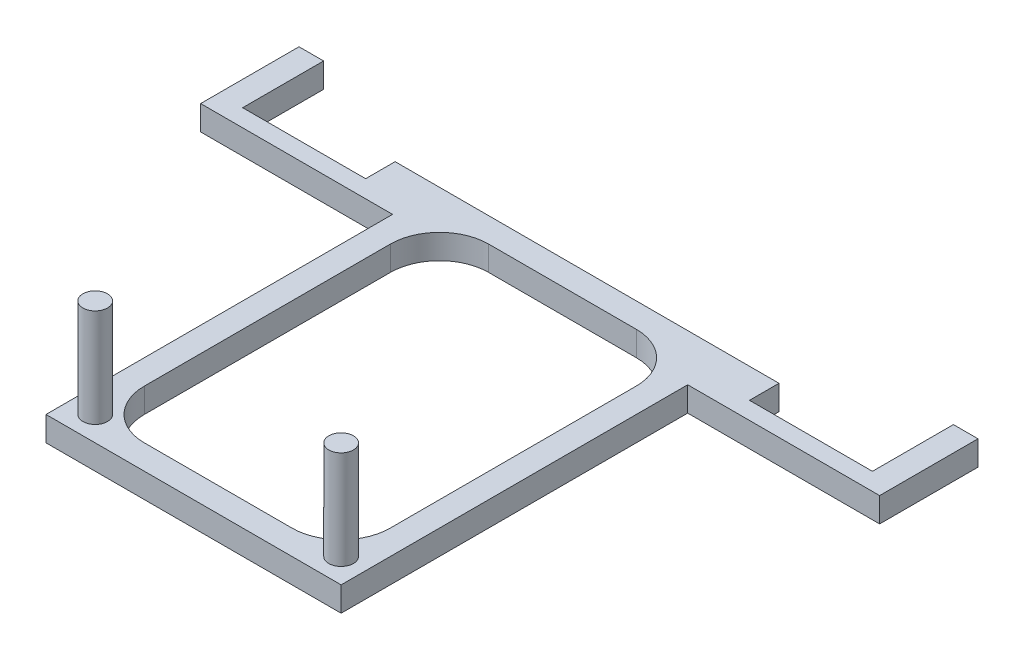
SolidWorks part; units mm, degrees
ref_plane "Front Plane" through (0, 0, 0) normal (0, 0, 1) x (1, 0, 0)
ref_plane "Top Plane" through (0, 0, 0) normal (0, 1, 0) x (1, 0, 0)
ref_plane "Right Plane" through (0, 0, 0) normal (1, 0, 0) x (0, 0, -1)
sketch "Sketch1" plane through (0, 0, 0) normal (0, 1, 0) x (1, 0, 0)
  line L1 (7.62, -10.16) -> (-7.62, -10.16)
  line L3 (7.62, 10.16) -> (-7.62, 10.16)
  line L5 (7.62, -10.16) -> (-7.62, 10.16) construction
  line L6 (7.62, 10.16) -> (-7.62, -10.16) construction
  line L7 (-17.5311, 10.2765) -> (-17.5311, 7.7365)
  line L8 (-17.5311, 7.7365) -> (-7.62, 7.7365)
  line L13 (-7.62, 7.7365) -> (-7.62, -10.16)
  line L14 (-17.5311, 10.2765) -> (-17.5311, 12.8165)
  line L16 (-17.5311, 12.8165) -> (-16.2611, 12.8165)
  line L17 (-16.2611, 12.8165) -> (-16.2611, 10.16)
  line L22 (0, 10.16) -> (0, -10.16) construction
  line L23 (-16.2611, 10.16) -> (-16.2611, 8.636)
  line L24 (-16.2611, 8.636) -> (-9.9111, 8.636)
  line L26 (-9.9111, 10.16) -> (-7.62, 10.16)
  line L27 (-9.9111, 10.16) -> (-9.9111, 8.636)
  line L28 (17.5311, 12.8165) -> (16.2611, 12.8165)
  line L29 (17.5311, 10.2765) -> (17.5311, 12.8165)
  line L30 (17.5311, 10.2765) -> (17.5311, 7.7365)
  line L31 (16.2611, 10.16) -> (16.2611, 8.636)
  line L32 (16.2611, 12.8165) -> (16.2611, 10.16)
  line L33 (17.5311, 7.7365) -> (7.62, 7.7365)
  line L34 (16.2611, 8.636) -> (9.9111, 8.636)
  line L35 (7.62, 10.16) -> (9.9111, 10.16)
  line L36 (9.9111, 10.16) -> (9.9111, 8.636)
  line L37 (7.62, 7.7365) -> (7.62, -10.16)
  point P0 (0, 0)
  point P9 (0, 10.16)
  dimension "D1" = 15.24
  dimension "D2" = 20.32
  dimension "D3" = 9.9111
  dimension "D4" = 2.54
  dimension "D5" = 2.54
  dimension "D6" = 1.27
  dimension "D7" = 6.35
  dimension "D8" = 6.35
  dimension "D9" = 1.524
  dimension "D10" = 1.524
  dimension "D11" = 15.24
  dimension "D12" = 7.7365
extrude "Boss-Extrude2" add sketch "Sketch1" along normal blind 1.27
sketch "Sketch3" plane through (0, 0, 0) normal (0, 1, 0) x (1, 0, 0)
  line L0 (-7.62, 7.7365) -> (-7.62, -10.16) construction
  line L1 (-7.62, -10.16) -> (7.62, -10.16) construction
  circle A0 centre (-6.35, -8.89) radius 0.635
  circle A1 centre (6.35, -8.89) radius 0.635
  dimension "D4" = 1.27
  dimension "D5" = 1.27
  dimension "D6" = 1.27
  dimension "D1" = 12.7
  dimension "D2" = 1.27
  dimension "D3" = 1.27
extrude "Boss-Extrude3" add sketch "Sketch3" along normal blind 6.35
sketch "Sketch4" plane through (0, 0, 0) normal (0, 1, 0) x (1, 0, 0)
  line L0 (0, 10.16) -> (0, -10.16) construction
  line L1 (9.9111, 10.16) -> (-9.9111, 10.16) construction
  line L2 (-7.62, -10.16) -> (7.62, -10.16) construction
  line L4 (3.81, -8.89) -> (-3.81, -8.89)
  line L5 (6.35, -6.35) -> (6.35, 6.35)
  line L6 (3.81, 8.89) -> (-3.81, 8.89)
  line L7 (-6.35, -6.35) -> (-6.35, 6.35)
  line L8 (6.35, -8.89) -> (-6.35, 8.89) construction
  line L9 (6.35, 8.89) -> (-6.35, -8.89) construction
  arc A0 (-3.81, -8.89) -> (-6.35, -6.35) centre (-3.81, -6.35) cw
  arc A1 (3.81, -8.89) -> (6.35, -6.35) centre (3.81, -6.35) ccw
  arc A2 (6.35, 6.35) -> (3.81, 8.89) centre (3.81, 6.35) ccw
  arc A3 (-3.81, 8.89) -> (-6.35, 6.35) centre (-3.81, 6.35) ccw
  point P6 (0, 0)
  dimension "D3" = 2.54
  dimension "D1" = 17.78
  dimension "D2" = 12.7
extrude "Cut-Extrude1" cut sketch "Sketch4" against normal blind 6.35 and the other way blind 6.35
